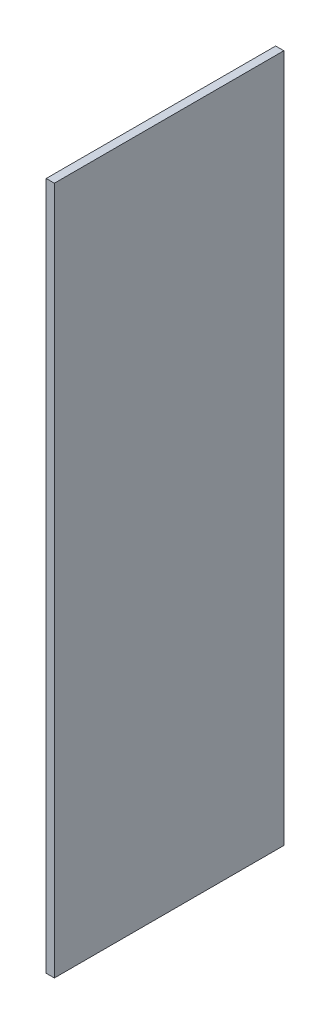
SolidWorks part; units mm, degrees
material "PC High Viscosity"
ref_plane "Front Plane" through (0, 0, 0) normal (0, 0, 1) x (1, 0, 0)
ref_plane "Top Plane" through (0, 0, 0) normal (0, 1, 0) x (1, 0, 0)
ref_plane "Right Plane" through (0, 0, 0) normal (1, 0, 0) x (0, 0, -1)
sketch "Sketch1" plane through (0, 0, 0) normal (1, 0, 0) x (0, 0, -1)
  line L0 (0, 0) -> (88.9, 0)
  line L1 (0, 0) -> (0, 266.7)
  line L2 (88.9, 0) -> (88.9, 266.7)
  line L3 (0, 266.7) -> (88.9, 266.7)
  dimension "D1" = 88.9
  dimension "D2" = 266.7
extrude "Boss-Extrude1" add sketch "Sketch1" along normal blind 3.175
